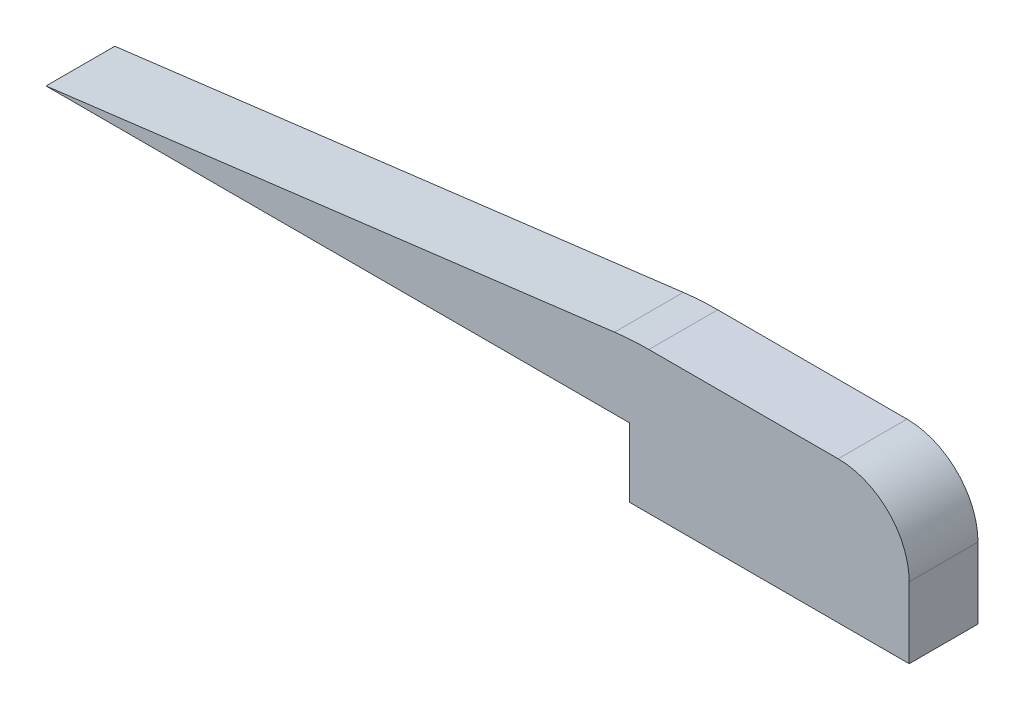
SolidWorks part; units mm, degrees
ref_plane "Front Plane" through (0, 0, 0) normal (0, 0, 1) x (1, 0, 0)
ref_plane "Top Plane" through (0, 0, 0) normal (0, 1, 0) x (1, 0, 0)
ref_plane "Right Plane" through (0, 0, 0) normal (1, 0, 0) x (0, 0, -1)
sketch "Sketch1" plane through (0, 0, 0) normal (0, 0, 1) x (1, 0, 0)
  line L0 (0, 0) -> (24.6154, 3.0769) construction
  line L1 (26.1907, 3.175) -> (34.925, 3.175) construction
  line L4 (38.1, -3.175) -> (25.4, -3.175) construction
  line L5 (25.4, -3.175) -> (25.4, 0) construction
  line L6 (25.4, 0) -> (0, 0) construction
  line L7 (38.1, 0) -> (38.1, -3.175) construction
  line L8 (38.2016, 0) -> (38.2016, -3.2766)
  line L9 (38.2016, -3.2766) -> (25.2984, -3.2766)
  line L10 (25.2984, -3.2766) -> (25.2984, -0.1016)
  line L11 (25.2984, -0.1016) -> (-1.6319, -0.1016)
  line L12 (-1.6319, -0.1016) -> (24.6028, 3.1777)
  line L13 (26.1907, 3.2766) -> (34.925, 3.2766)
  arc A0 (24.6154, 3.0769) -> (26.1907, 3.175) centre (26.1907, -9.525) cw construction
  arc A2 (34.925, 3.175) -> (38.1, 0) centre (34.925, 0) cw construction
  arc A3 (24.6028, 3.1777) -> (26.1907, 3.2766) centre (26.1907, -9.525) cw
  arc A4 (34.925, 3.2766) -> (38.2016, 0) centre (34.925, 0) cw
  point P11 (25.4, 3.175)
  dimension "D1" = 12.7
  dimension "D2" = 3.175
  dimension "D6" = 3.175
  dimension "D3" = 25.4
  dimension "D4" = 3.175
  dimension "D5" = 12.7
  dimension "D7" = 0.1016
extrude "Boss-Extrude1" add sketch "Sketch1" along normal blind 3.175
